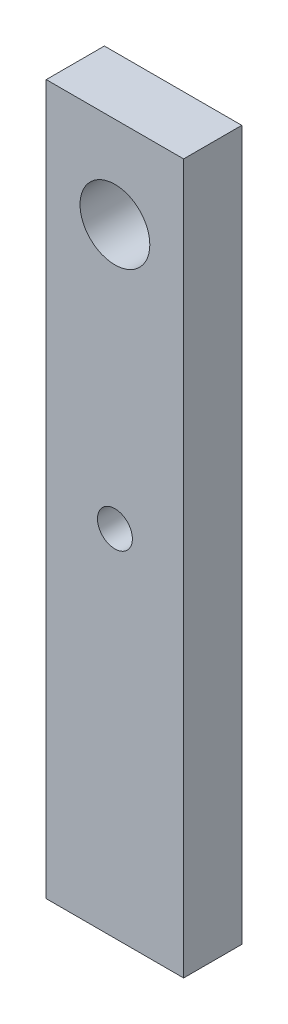
SolidWorks part; units mm, degrees
material "ABS"
ref_plane "Front Plane" through (0, 0, 0) normal (0, 0, 1) x (1, 0, 0)
ref_plane "Top Plane" through (0, 0, 0) normal (0, 1, 0) x (1, 0, 0)
ref_plane "Right Plane" through (0, 0, 0) normal (1, 0, 0) x (0, 0, -1)
sketch "Sketch1" plane through (0, 0, 0) normal (0, 0, 1) x (1, 0, 0)
  line L1 (-11.8132, -60.9892) -> (11.8132, -60.9892)
  line L2 (-11.8132, -60.9892) -> (-11.8132, 60.9892)
  line L3 (-11.8132, 60.9892) -> (11.8132, 60.9892)
  line L4 (11.8132, -60.9892) -> (11.8132, 60.9892)
  line L5 (-11.8132, -60.9892) -> (11.8132, 60.9892) construction
  line L6 (-11.8132, 60.9892) -> (11.8132, -60.9892) construction
  circle A0 centre (0, 0) radius 3
  circle A1 centre (0, 45.2995) radius 6
  point P0 (0, 0)
extrude "Boss-Extrude1" add sketch "Sketch1" along normal blind 10
